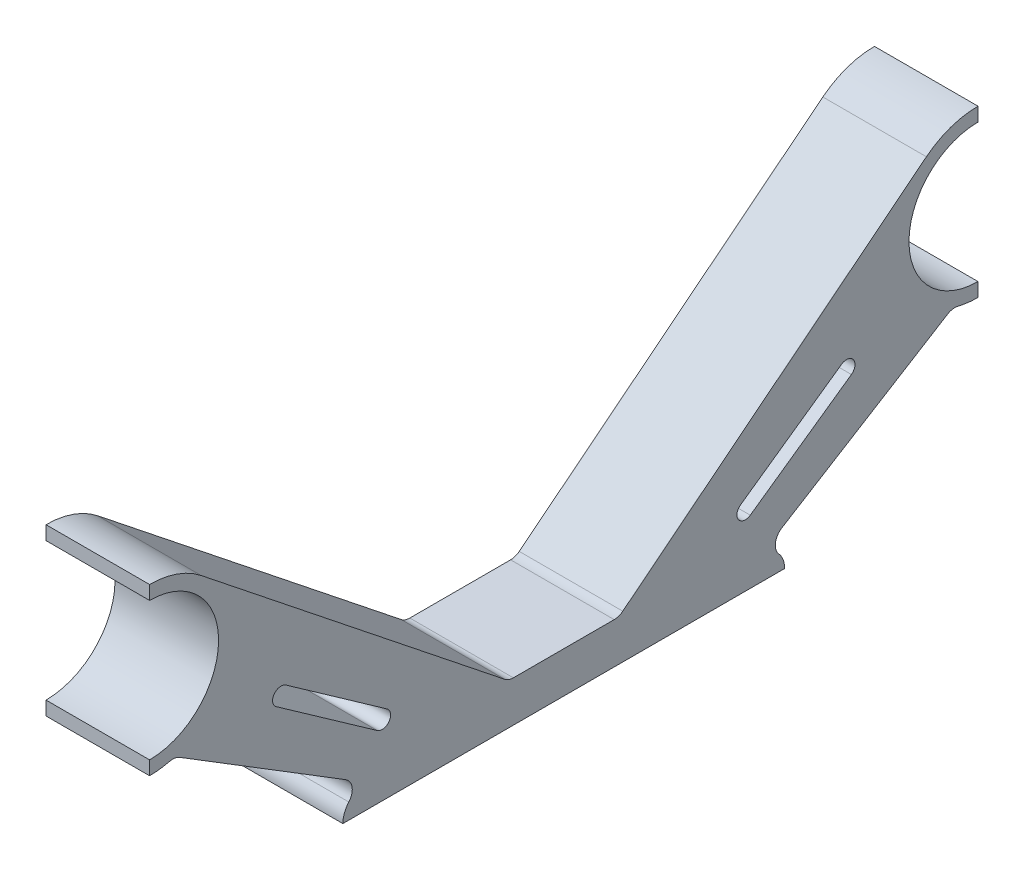
SolidWorks part; units mm, degrees
ref_plane "Piano frontale" through (0, 0, 0) normal (0, 0, 1) x (1, 0, 0)
ref_plane "Piano superiore" through (0, 0, 0) normal (0, 1, 0) x (1, 0, 0)
ref_plane "Piano destro" through (0, 0, 0) normal (1, 0, 0) x (0, 0, -1)
sketch "Schizzo1" plane through (0, 0, 0) normal (1, 0, 0) x (0, 0, -1)
  line L0 (0, 55) -> (0, -55) construction
  line L1 (-30, 22) -> (-30, 21)
  line L2 (-30, 11) -> (-30, 10)
  line L3 (16, 0) -> (-16, 0)
  line L4 (55, 0) -> (-55, 0) construction
  line L5 (-14.2798, 1.7202) -> (-28.1739, 10.2846)
  line L6 (4, 2.9702) -> (-4, 2.9702)
  line L7 (-4, 2.9702) -> (-26.263, 20.6941)
  line L8 (4, 2.9702) -> (26.263, 20.6941)
  line L9 (14.2798, 1.7202) -> (28.1739, 10.2846)
  line L10 (30, 11) -> (30, 10)
  line L11 (30, 22) -> (30, 21)
  line L12 (-20.4785, 10.2541) -> (-13.1538, 5.093) construction
  line L13 (-20.1258, 10.7548) -> (-12.801, 5.5937)
  line L14 (-20.8313, 9.7535) -> (-13.5065, 4.5924)
  line L15 (20.4785, 10.2541) -> (13.1538, 5.093) construction
  line L16 (20.1258, 10.7548) -> (12.801, 5.5937)
  line L17 (20.8313, 9.7535) -> (13.5065, 4.5924)
  arc A0 (-30, 11) -> (-30, 21) centre (-30, 16) ccw
  arc A1 (-30, 10) -> (-28.1739, 10.2846) centre (-30, 16) ccw
  arc A2 (-14.2798, 1.7202) -> (-16, 0) centre (-14.2798, 0) ccw
  arc A3 (14.2798, 1.7202) -> (16, 0) centre (14.2798, 0) cw
  arc A4 (30, 10) -> (28.1739, 10.2846) centre (30, 16) cw
  arc A5 (30, 11) -> (30, 21) centre (30, 16) cw
  arc A6 (-26.263, 20.6941) -> (-30, 22) centre (-30, 16) ccw
  arc A7 (26.263, 20.6941) -> (30, 22) centre (30, 16) cw
  arc A8 (-20.1258, 10.7548) -> (-20.8313, 9.7535) centre (-20.4785, 10.2541) ccw
  arc A9 (-13.5065, 4.5924) -> (-12.801, 5.5937) centre (-13.1538, 5.093) ccw
  arc A10 (20.1258, 10.7548) -> (20.8313, 9.7535) centre (20.4785, 10.2541) cw
  arc A11 (13.5065, 4.5924) -> (12.801, 5.5937) centre (13.1538, 5.093) cw
  point P8 (-16.8162, 7.6736)
  point P29 (0, 2.9702)
  point P31 (0, 0)
  point P38 (16.8162, 7.6736)
  dimension "D1" = 10
  dimension "D3" = 12
  dimension "D2" = 30
  dimension "D4" = 16
  dimension "D5" = 16
  dimension "D6" = 4
extrude "Estrusione-Estrusione1" add sketch "Schizzo1" along normal mid plane 7.5
fillet "Raccordo2" radius 1 6 edges at (0, 10.2846, 28.1739) (0, 10.2846, -28.1739) (0, 2.9702, 4) (0, 2.9702, -4) (0, 1.7202, -14.2798) (0, 1.7202, 14.2798)
